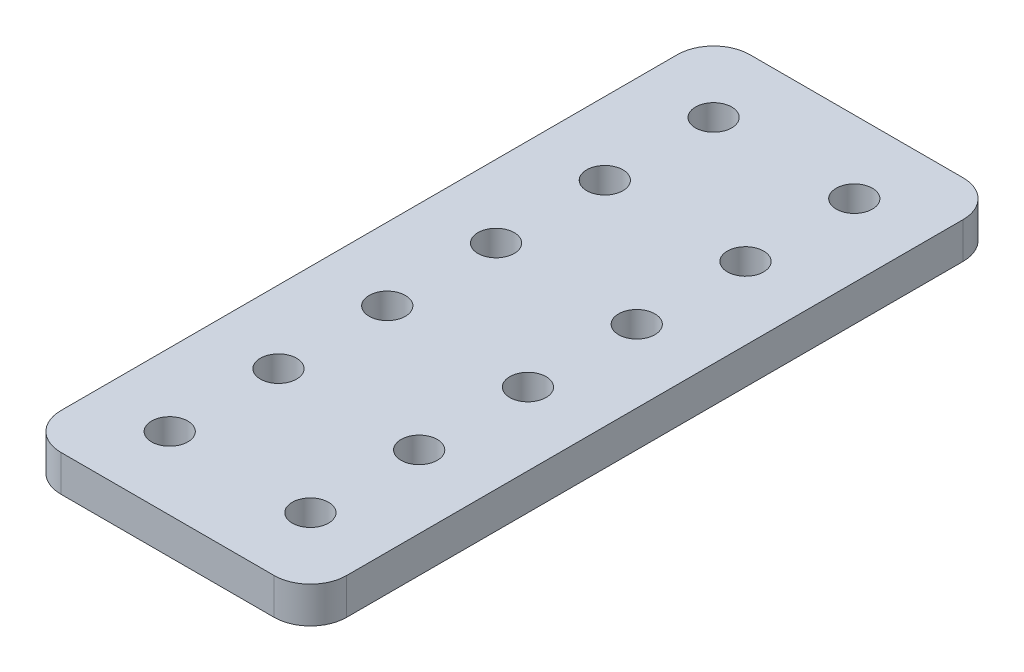
SolidWorks part; units mm, degrees
ref_plane "Front" through (0, 0, 0) normal (0, 0, 1) x (1, 0, 0)
ref_plane "Top" through (0, 0, 0) normal (0, 1, 0) x (1, 0, 0)
ref_plane "Right" through (0, 0, 0) normal (1, 0, 0) x (0, 0, -1)
sketch "Sketch1" plane through (0, 0, 0) normal (0, 1, 0) x (1, 0, 0)
  line L0 (-25.019, -47.625) -> (25.019, -47.625) construction
  line L1 (-25.019, -60.325) -> (25.019, -60.325)
  line L2 (-25.019, -60.325) -> (-25.019, 60.325)
  line L3 (-25.019, 60.325) -> (25.019, 60.325)
  line L4 (25.019, -60.325) -> (25.019, 60.325)
  line L5 (-25.019, -60.325) -> (25.019, 60.325) construction
  line L6 (-25.019, 60.325) -> (25.019, -60.325) construction
  circle A0 centre (12.319, -47.625) radius 3.175
  circle A1 centre (-12.319, -47.625) radius 3.175
  circle A4 centre (12.319, -28.575) radius 3.175
  circle A5 centre (-12.319, -28.575) radius 3.175
  circle A6 centre (12.319, -9.525) radius 3.175
  circle A7 centre (-12.319, -9.525) radius 3.175
  circle A8 centre (12.319, 9.525) radius 3.175
  circle A9 centre (-12.319, 9.525) radius 3.175
  circle A10 centre (12.319, 28.575) radius 3.175
  circle A11 centre (-12.319, 28.575) radius 3.175
  circle A12 centre (12.319, 47.625) radius 3.175
  circle A13 centre (-12.319, 47.625) radius 3.175
  point P0 (0, 0)
  dimension "D8" = 6.35
  dimension "D2" = 24.638
  dimension "D3" = 12.7
  dimension "D5" = 12.7
  dimension "D4" = 12.7
  dimension "D6" = 12.7
  dimension "D7" = 19.05
  dimension "D1" = 6
extrude "Boss-Extrude1" add sketch "Sketch1" along normal blind 6.35
fillet "Fillet1" radius 6.35 4 edges at (25.019, 3.175, 60.325) (-25.019, 3.175, 60.325) (-25.019, 3.175, -60.325) (25.019, 3.175, -60.325)
equation "\"D5@Sketch1\"=\"D4@Sketch1\""
equation "\"D4@Sketch1\"=\"D3@Sketch1\""
equation "\"D6@Sketch1\"=\"D3@Sketch1\""
